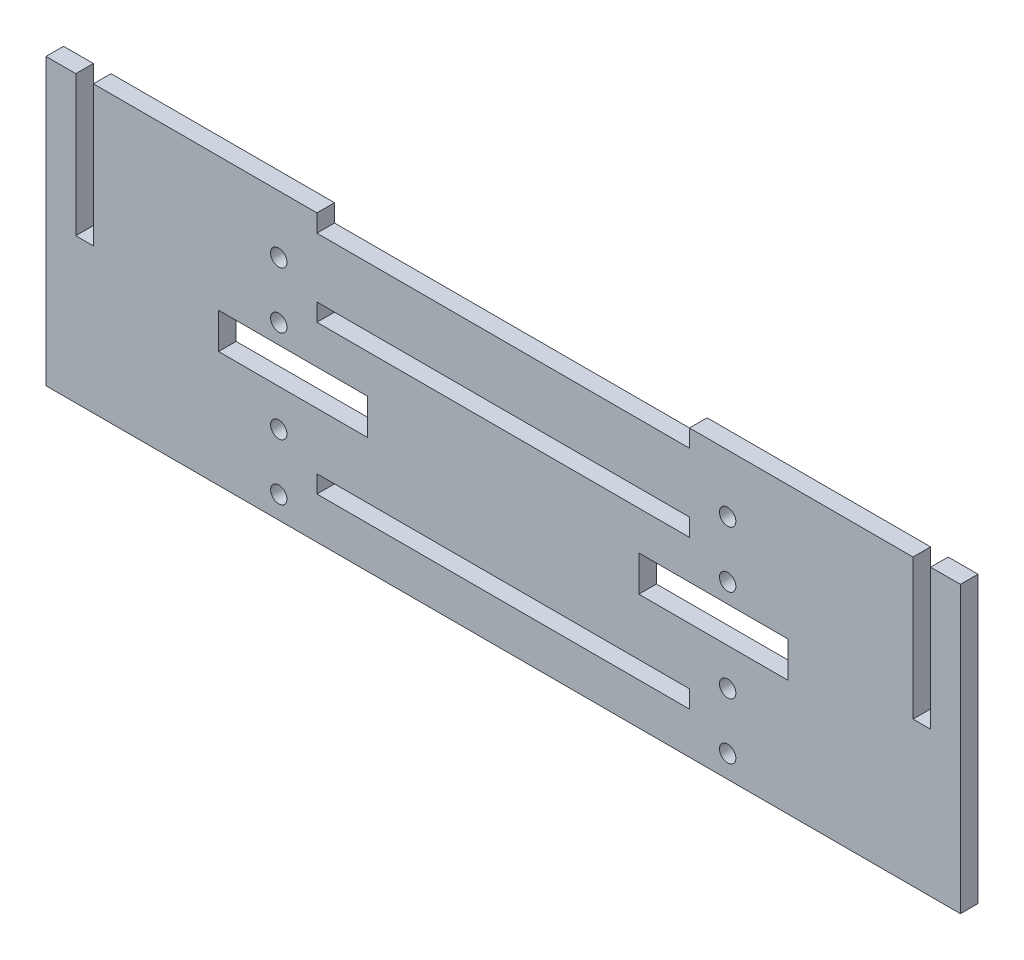
SolidWorks part; units mm, degrees
ref_plane "Front Plane" through (0, 0, 0) normal (0, 0, 1) x (1, 0, 0)
ref_plane "Top Plane" through (0, 0, 0) normal (0, 1, 0) x (1, 0, 0)
ref_plane "Right Plane" through (0, 0, 0) normal (1, 0, 0) x (0, 0, -1)
sketch "Sketch1" plane through (0, 0, 0) normal (0, 0, 1) x (1, 0, 0)
  line L0 (12.7, 34.6964) -> (127, 34.6964)
  line L1 (0, 0) -> (139.7, 0)
  line L2 (0, 0) -> (0, 47.8536)
  line L3 (0, 47.8536) -> (139.7, 47.8536)
  line L4 (139.7, 0) -> (139.7, 47.8536)
  line L5 (12.7, 9.3472) -> (127, 9.3472)
  line L6 (12.7, 9.3472) -> (12.7, 6.35)
  line L7 (12.7, 6.35) -> (127, 6.35)
  line L8 (127, 9.3472) -> (127, 6.35)
  line L9 (12.7, 34.6964) -> (12.7, 31.6992)
  line L10 (12.7, 31.6992) -> (127, 31.6992)
  line L11 (127, 34.6964) -> (127, 31.6992)
  line L12 (12.7, 47.8536) -> (127, 47.8536) construction
  line L13 (12.7, 47.8536) -> (12.7, 44.8564)
  line L14 (12.7, 44.8564) -> (127, 44.8564)
  line L15 (127, 47.8536) -> (127, 44.8564)
  line L16 (139.7, 23.9268) -> (142.6972, 23.9268)
  line L17 (142.6972, 23.9268) -> (142.6972, 47.8536)
  line L18 (142.6972, 47.8536) -> (147.7772, 47.8536)
  line L19 (147.7772, 47.8536) -> (147.7772, 0)
  line L20 (147.7772, 0) -> (139.7, 0)
  line L21 (69.85, 44.8564) -> (69.85, 34.6964) construction
  line L22 (-8.0772, 0) -> (0, 0)
  line L23 (0, 23.9268) -> (-2.9972, 23.9268)
  line L24 (-8.0772, 47.8536) -> (-8.0772, 0)
  line L25 (-2.9972, 47.8536) -> (-8.0772, 47.8536)
  line L26 (-2.9972, 23.9268) -> (-2.9972, 47.8536)
  dimension "D1" = 139.7
  dimension "D2" = 6.35
  dimension "D3" = 12.7
  dimension "D4" = 12.7
  dimension "D5" = 2.9972
  dimension "D7" = 22.352
  dimension "D8" = 5.08
  dimension "D9" = 2.9972
  dimension "D6" = 10.16
extrude "Boss-Extrude1" add sketch "Sketch1" along normal blind 2.9972 contours L20 L19 L18 L17 L16 L4 | L3 L15 L14 L13 L2 L1 L4 L0 L11 L10 L9 L5 L8 L7 L6 | L23 L26 L25 L24 L22 L2
sketch "Sketch2" plane through (0, 0, 0) normal (0, 0, -1) x (-1, 0, 0)
  line L0 (-69.85, 12.6492) -> (-69.85, 9.3472) construction
  line L2 (-12.7, 9.3472) -> (-127, 9.3472) construction
  line L3 (-108.1024, 12.6492) -> (-31.5976, 12.6492) construction
  line L4 (-101.6, 9.3472) -> (-38.1, 9.3472) construction
  line L5 (-108.1024, 37.9984) -> (-31.5976, 37.9984) construction
  line L6 (-69.85, 37.9984) -> (-69.85, 34.6964) construction
  line L7 (-12.7, 34.6964) -> (-127, 34.6964) construction
  circle A0 centre (-108.1024, 12.6492) radius 1.397
  circle A1 centre (-31.5976, 12.6492) radius 1.397
  circle A2 centre (-108.1024, 37.9984) radius 1.397
  circle A3 centre (-31.5976, 37.9984) radius 1.397
  dimension "D2" = 2.794
  dimension "D3" = 1.905
  dimension "D1" = 79.2988
extrude "Cut-Extrude1" cut sketch "Sketch2" against normal through all
sketch "Sketch3" plane through (0, 0, 0) normal (0, 0, -1) x (-1, 0, 0)
  line L0 (-12.7, 44.8564) -> (-127, 44.8564) construction
  line L1 (-127, 47.8536) -> (-101.6, 47.8536)
  line L2 (-127, 47.8536) -> (-127, 44.8564)
  line L3 (-127, 44.8564) -> (-101.6, 44.8564)
  line L4 (-101.6, 47.8536) -> (-101.6, 44.8564)
  line L5 (-12.7, 31.6992) -> (-127, 31.6992) construction
  line L6 (-127, 34.6964) -> (-101.6, 34.6964)
  line L7 (-127, 34.6964) -> (-127, 31.6992)
  line L8 (-127, 31.6992) -> (-101.6, 31.6992)
  line L9 (-101.6, 34.6964) -> (-101.6, 31.6992)
  line L10 (-12.7, 6.35) -> (-127, 6.35) construction
  line L11 (-127, 9.3472) -> (-101.6, 9.3472)
  line L12 (-127, 9.3472) -> (-127, 6.35)
  line L13 (-127, 6.35) -> (-101.6, 6.35)
  line L14 (-101.6, 9.3472) -> (-101.6, 6.35)
  line L15 (-69.85, 0) -> (-69.85, 44.8564) construction
  line L16 (-147.7772, 0) -> (8.0772, 0) construction
  line L17 (-38.1, 9.3472) -> (-38.1, 6.35)
  line L18 (-12.7, 6.35) -> (-38.1, 6.35)
  line L19 (-12.7, 9.3472) -> (-12.7, 6.35)
  line L20 (-12.7, 9.3472) -> (-38.1, 9.3472)
  line L21 (-38.1, 34.6964) -> (-38.1, 31.6992)
  line L22 (-12.7, 31.6992) -> (-38.1, 31.6992)
  line L23 (-12.7, 34.6964) -> (-12.7, 31.6992)
  line L24 (-12.7, 34.6964) -> (-38.1, 34.6964)
  line L25 (-38.1, 47.8536) -> (-38.1, 44.8564)
  line L26 (-12.7, 44.8564) -> (-38.1, 44.8564)
  line L27 (-12.7, 47.8536) -> (-12.7, 44.8564)
  line L28 (-12.7, 47.8536) -> (-38.1, 47.8536)
  dimension "D1" = 25.4
extrude "Boss-Extrude2" add sketch "Sketch3" against normal up to vertex (2.9972 mm away) up to point (127, 47.8536, 2.9972)
sketch "Sketch4" plane through (0, 0, 0) normal (0, 0, -1) x (-1, 0, 0)
  line L1 (-147.7772, 0) -> (8.0772, 0)
  line L2 (-147.7772, 0) -> (-147.7772, -0.762)
  line L3 (-147.7772, -0.762) -> (8.0772, -0.762)
  line L4 (8.0772, 0) -> (8.0772, -0.762)
  dimension "D1" = 0.762
extrude "Boss-Extrude3" add sketch "Sketch4" against normal up to vertex (2.9972 mm away)
sketch "Sketch5" plane through (0, 0, 2.9972) normal (0, 0, 1) x (1, 0, 0)
  line L1 (108.1024, 12.6492) -> (31.5976, 12.6492) construction
  line L3 (69.85, 28.3972) -> (69.85, 34.6964) construction
  line L4 (38.1, 34.6964) -> (101.6, 34.6964) construction
  line L7 (108.1024, 12.6492) -> (108.1024, 9.3472) construction
  line L8 (139.7, 9.3472) -> (101.6, 9.3472) construction
  line L9 (31.5976, 28.3972) -> (108.1024, 28.3972) construction
  line L11 (31.5976, 31.6992) -> (38.1, 31.6992) construction
  line L14 (108.1024, 9.3472) -> (101.6, 9.3472) construction
  line L15 (31.5976, 12.6492) -> (31.5976, 6.35) construction
  line L16 (38.1, 6.35) -> (0, 6.35) construction
  line L17 (31.5976, 6.35) -> (38.1, 6.35) construction
  circle A0 centre (31.5976, 28.3972) radius 1.397
  circle A1 centre (108.1024, 28.3972) radius 1.397
  circle A2 centre (31.5976, 37.9984) radius 1.397 construction
  circle A3 centre (108.1024, 37.9984) radius 1.397 construction
  circle A4 centre (31.5976, 12.6492) radius 1.397 construction
extrude "Cut-Extrude2" cut sketch "Sketch5" against normal through all
sketch "Sketch6" plane through (0, 0, 2.9972) normal (0, 0, 1) x (1, 0, 0)
  line L0 (0, 23.9268) -> (0, 47.8536) construction
  line L1 (21.336, 25.0952) -> (46.736, 25.0952)
  line L2 (21.336, 25.0952) -> (21.336, 18.9992)
  line L3 (21.336, 18.9992) -> (46.736, 18.9992)
  line L4 (46.736, 25.0952) -> (46.736, 18.9992)
  line L5 (69.85, 31.6992) -> (69.85, 9.3472) construction
  line L6 (38.1, 31.6992) -> (101.6, 31.6992) construction
  line L7 (92.964, 25.0952) -> (92.964, 18.9992)
  line L8 (118.364, 18.9992) -> (92.964, 18.9992)
  line L11 (38.1, 9.3472) -> (101.6, 9.3472) construction
  line L13 (118.364, 25.0952) -> (118.364, 18.9992)
  line L14 (118.364, 25.0952) -> (92.964, 25.0952)
  dimension "D1" = 21.336
  dimension "D3" = 25.4
  dimension "D5" = 6.096
  dimension "D6" = 9.652
sketch "Sketch7" plane through (0, 0, 0) normal (0, 0, -1) x (-1, 0, 0)
  line L0 (-108.1024, 12.6492) -> (-108.1024, 3.048) construction
  line L1 (-31.5976, 3.048) -> (-31.5976, 12.6492) construction
  line L2 (-31.5976, 3.048) -> (-108.1024, 3.048) construction
  line L3 (-101.6, 7.8486) -> (-108.1024, 7.8486) construction
  line L4 (-101.6, 6.35) -> (-101.6, 9.3472) construction
  circle A0 centre (-108.1024, 3.048) radius 1.397
  circle A1 centre (-31.5976, 3.048) radius 1.397
  circle A2 centre (-108.1024, 12.6492) radius 1.397 construction
extrude "Cut-Extrude3" cut sketch "Sketch7" against normal through all
extrude "Cut-Extrude4" cut sketch "Sketch6" against normal through all
